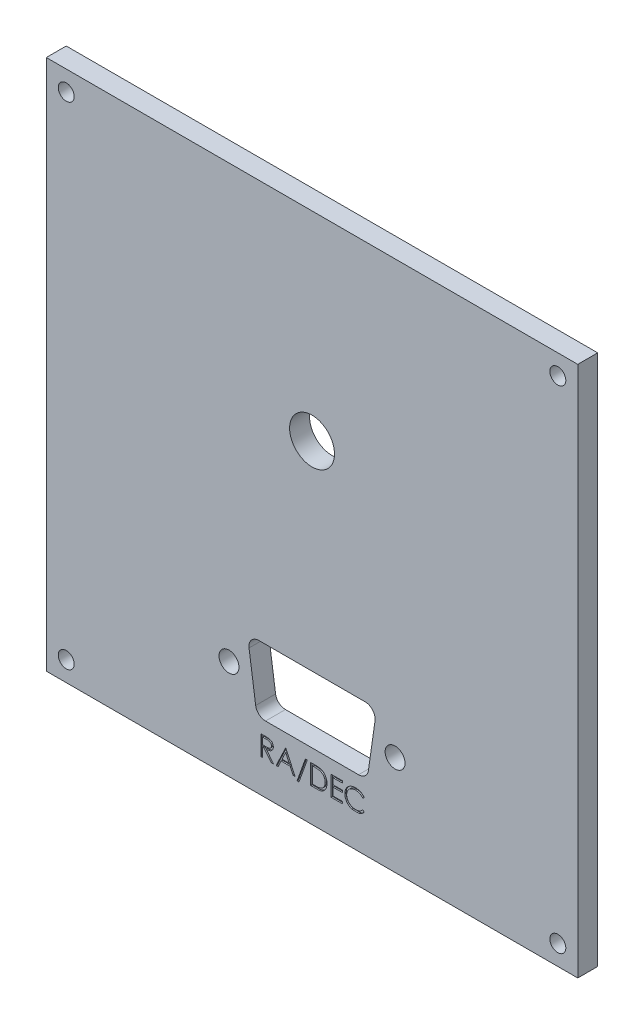
SolidWorks part; units mm, degrees
material "5052-O"
ref_plane "정면" through (0, 0, 0) normal (0, 0, 1) x (1, 0, 0)
ref_plane "윗면" through (0, 0, 0) normal (0, 1, 0) x (1, 0, 0)
ref_plane "우측면" through (0, 0, 0) normal (1, 0, 0) x (0, 0, -1)
sketch "스케치1" plane through (0, 0, 0) normal (0, 0, 1) x (1, 0, 0)
  line L1 (-40, 40) -> (40, 40)
  line L2 (-40, 40) -> (-40, -40)
  line L3 (-40, -40) -> (40, -40)
  line L4 (40, 40) -> (40, -40)
  line L5 (-40, 40) -> (40, -40) construction
  line L6 (-40, -40) -> (40, 40) construction
  point P0 (0, 0)
  dimension "D1" = 80
  dimension "D2" = 80
extrude "보스-돌출1" add sketch "스케치1" along normal blind 3
hole_wizard "M2 여유 구멍1" positions "스케치2" profile "스케치3" hole size "M2" standard "ISO" end condition through all
sketch "스케치2" plane through (0, 0, 3) normal (0, 0, 1) x (1, 0, 0)
  line L1 (-37, 37) -> (37, 37)
  line L2 (-37, 37) -> (-37, -37)
  line L3 (-37, -37) -> (37, -37)
  line L4 (37, 37) -> (37, -37)
  line L5 (40, 40) -> (-40, 40) construction
  line L6 (-40, 40) -> (-40, -40) construction
  point P0 (-37, 37)
  point P2 (-37, -37)
  point P4 (37, -37)
  point P6 (37, 37)
  point P92 (0, 37)
  point P93 (0, 40)
  point P94 (-37, 0)
  point P97 (-40, 0)
  dimension "D1" = 74
  dimension "D2" = 74
sketch "스케치3" plane through (-37, 37, 3) normal (1, 0, 0) x (0, -1, 0)
  line L0 (0, 0) -> (0, 3)
  line L1 (0, 3) -> (1.2, 3)
  line L2 (1.2, 3) -> (1.2, 0)
  line L5 (1.2, 0) -> (0, 0)
  line L11 (0, -6.35) -> (0, 107.95) construction
  dimension "관통 구멍 지름" = 2.4
  dimension "관통 구멍 깊이" = 3
hole_wizard "M3 여유 구멍1" positions "스케치4" profile "스케치5" hole size "M3" standard "ISO"
sketch "스케치4" plane through (0, 0, 3) normal (0, 0, 1) x (1, 0, 0)
  line L1 (5.1764, 29.3185) -> (-19.3185, 4.8236)
  line L2 (-19.3185, 4.8236) -> (14.1421, -4.1421)
  line L3 (14.1421, -4.1421) -> (5.1764, 29.3185)
  line L4 (5.1764, 29.3185) -> (-2.5882, 0.3407)
  line L7 (-40, 40) -> (-40, -40) construction
  line L8 (40, 40) -> (-40, 40) construction
  circle A0 centre (0, 10) radius 20 construction
  point P3 (5.1764, 29.3185)
  point P4 (-19.3185, 4.8236)
  point P5 (14.1421, -4.1421)
  point P27 (-5.1764, 127.2034)
  dimension "D1" = 40
  dimension "D2" = 15
  dimension "D3" = 30
sketch "스케치5" plane through (-5.1764, 127.2034, 3) normal (1, 0, 0) x (0, -1, 0)
  line L0 (0, 0) -> (0, 3)
  line L1 (0, 3) -> (1.6, 3)
  line L2 (1.6, 3) -> (1.6, 0)
  line L5 (1.6, 0) -> (0, 0)
  line L11 (0, -6.35) -> (0, 107.95) construction
  dimension "관통 구멍 지름" = 3.2
  dimension "관통 구멍 깊이" = 3
sketch "스케치6" plane through (0, 0, 3) normal (0, 0, 1) x (1, 0, 0)
  line L0 (-8, -20) -> (8, -20)
  line L1 (8.4849, -28.7121) -> (9.4849, -21.7121)
  line L2 (7, -30) -> (-7, -30)
  line L3 (-8.4849, -28.7121) -> (-9.4849, -21.7121)
  line L4 (-40, -40) -> (40, -40) construction
  line L5 (-12.5, -25) -> (12.5, -25)
  line L6 (0, -20) -> (0, -30)
  line L7 (40, -40) -> (40, 40) construction
  circle A0 centre (-8, -21.5) radius 1.5
  circle A1 centre (8, -21.5) radius 1.5
  circle A2 centre (-7, -28.5) radius 1.5
  circle A3 centre (7, -28.5) radius 1.5
  circle A4 centre (-12.5, -25) radius 1.5
  circle A5 centre (12.5, -25) radius 1.5
  point P18 (0, -25)
  dimension "D1" = 3
  dimension "D2" = 16
  dimension "D3" = 14
  dimension "D4" = 7
  dimension "D7" = 3
  dimension "D5" = 10
  dimension "D6" = 25
  dimension "D8" = 40
extrude "컷-돌출1" cut sketch "스케치6" against normal through all
sketch "스케치7" plane through (0, 0, 3) normal (0, 0, 1) x (1, 0, 0)
  line L0 (-10, -35) -> (10, -35)
  line L1 (-40, -40) -> (40, -40) construction
  line L2 (-7.7115, -32) -> (-7.1112, -32)
  line L3 (-6.8906, -33.6154) -> (-5.7885, -35)
  line L4 (-5.7885, -35) -> (-6.1214, -35)
  line L5 (-6.1214, -35) -> (-7.2236, -33.6154)
  line L6 (-7.2236, -33.6154) -> (-7.4423, -33.6154)
  line L7 (-7.4423, -33.6154) -> (-7.4423, -35)
  line L8 (-7.4423, -35) -> (-7.7115, -35)
  line L9 (-7.7115, -35) -> (-7.7115, -32)
  line L10 (-7.4423, -32.3077) -> (-7.4423, -33.3077)
  line L11 (-7.4423, -33.3077) -> (-6.893, -33.3119)
  line L12 (-6.8798, -32.3077) -> (-7.4423, -32.3077)
  line L13 (-3.9423, -32) -> (-2.5577, -35)
  line L14 (-2.5577, -35) -> (-2.8504, -35)
  line L15 (-2.8504, -35) -> (-3.2939, -34.0385)
  line L16 (-3.2939, -34.0385) -> (-4.6538, -34.0385)
  line L17 (-4.6538, -34.0385) -> (-5.11, -35)
  line L18 (-5.11, -35) -> (-5.4038, -35)
  line L19 (-5.4038, -35) -> (-3.9808, -32)
  line L20 (-3.9808, -32) -> (-3.9423, -32)
  line L21 (-3.9645, -32.5847) -> (-4.5078, -33.7308)
  line L22 (-4.5078, -33.7308) -> (-3.4357, -33.7308)
  line L23 (-3.4357, -33.7308) -> (-3.9645, -32.5847)
  line L24 (-0.7115, -31.9231) -> (-1.9663, -35.4231)
  line L25 (-1.9663, -35.4231) -> (-2.25, -35.4231)
  line L26 (-2.25, -35.4231) -> (-0.9952, -31.9231)
  line L27 (-0.9952, -31.9231) -> (-0.7115, -31.9231)
  line L28 (-0.2115, -35) -> (-0.2115, -32)
  line L29 (-0.2115, -32) -> (0.3942, -32)
  line L30 (0.7181, -35) -> (-0.2115, -35)
  line L31 (0.0577, -34.6923) -> (0.402, -34.6923)
  line L32 (0.2686, -32.3077) -> (0.0577, -32.3077)
  line L33 (0.0577, -32.3077) -> (0.0577, -34.6923)
  line L34 (2.8654, -32) -> (4.5577, -32)
  line L35 (4.5577, -32) -> (4.5577, -32.3077)
  line L36 (4.5577, -32.3077) -> (3.1346, -32.3077)
  line L37 (3.1346, -32.3077) -> (3.1346, -33.2308)
  line L38 (3.1346, -33.2308) -> (4.5577, -33.2308)
  line L39 (4.5577, -33.2308) -> (4.5577, -33.5385)
  line L40 (4.5577, -33.5385) -> (3.1346, -33.5385)
  line L41 (3.1346, -33.5385) -> (3.1346, -34.6923)
  line L42 (3.1346, -34.6923) -> (4.5577, -34.6923)
  line L43 (4.5577, -34.6923) -> (4.5577, -35)
  line L44 (4.5577, -35) -> (2.8654, -35)
  line L45 (2.8654, -35) -> (2.8654, -32)
  line L46 (7.8654, -32.5505) -> (7.6298, -32.7308)
  line L47 (7.6298, -34.2692) -> (7.8654, -34.4477)
  spline S0 degree 3 poles (-7.1112, -32) (-7.0343, -32.0004) (-6.924, -32.0002) (-6.7838, -32.0059) (-6.6938, -32.0094) (-6.6139, -32.0159) (-6.5272, -32.0234) (-6.4676, -32.0328) (-6.4315, -32.0409) knots 0 0 0 0 0.338434 0.484822 0.617158 0.734698 0.837385 1 1 1 1
  spline S1 degree 3 poles (-6.4315, -32.0409) (-6.3878, -32.0505) (-6.3243, -32.0705) (-6.244, -32.106) (-6.1876, -32.1368) (-6.1347, -32.1724) (-6.0847, -32.2122) (-6.0374, -32.256) (-5.9948, -32.3049) (-5.9545, -32.3562) (-5.9206, -32.4117) (-5.8913, -32.4697) (-5.868, -32.5308) (-5.8493, -32.5944) (-5.8313, -32.6848) (-5.8268, -32.7549) (-5.8269, -32.8023) knots 0 0 0 0 0.127064 0.188745 0.249132 0.309453 0.369827 0.43065 0.492352 0.554072 0.61569 0.676798 0.738439 0.801317 0.865185 1 1 1 1
  spline S2 degree 3 poles (-5.8269, -32.8023) (-5.8266, -32.8801) (-5.8399, -32.9957) (-5.8911, -33.139) (-5.9428, -33.2369) (-6.0086, -33.3251) (-6.0878, -33.4026) (-6.1802, -33.4674) (-6.2663, -33.5124) (-6.3423, -33.5412) (-6.4049, -33.5614) (-6.4732, -33.5771) (-6.5466, -33.5911) (-6.6252, -33.6017) (-6.7403, -33.6124) (-6.8295, -33.6152) (-6.8906, -33.6154) knots 0 0 0 0 0.153721 0.226714 0.299191 0.37119 0.443006 0.516689 0.593217 0.633873 0.676989 0.7229 0.771959 0.824211 0.879379 1 1 1 1
  spline S3 degree 3 poles (-6.893, -33.3119) (-6.8433, -33.3127) (-6.7714, -33.3101) (-6.6788, -33.3046) (-6.6171, -33.2987) (-6.5605, -33.291) (-6.5091, -33.2814) (-6.4629, -33.2702) (-6.409, -33.2529) (-6.3488, -33.2254) (-6.2834, -33.1855) (-6.2276, -33.1353) (-6.1806, -33.0779) (-6.1428, -33.0148) (-6.1069, -32.9237) (-6.096, -32.8507) (-6.0962, -32.8017) knots 0 0 0 0 0.138913 0.201185 0.259124 0.312255 0.360682 0.405086 0.445102 0.518778 0.589462 0.658462 0.727283 0.796322 0.863175 1 1 1 1
  spline S4 degree 3 poles (-6.0962, -32.8017) (-6.0963, -32.754) (-6.1062, -32.682) (-6.1441, -32.5937) (-6.1821, -32.5318) (-6.2284, -32.4757) (-6.2826, -32.4277) (-6.3434, -32.388) (-6.4002, -32.3627) (-6.451, -32.3472) (-6.4951, -32.3362) (-6.5449, -32.3274) (-6.6007, -32.3204) (-6.6622, -32.3144) (-6.7559, -32.3087) (-6.8291, -32.3075) (-6.8798, -32.3077) knots 0 0 0 0 0.136365 0.204019 0.273064 0.342913 0.410965 0.479169 0.549308 0.587652 0.630647 0.678879 0.731934 0.791111 0.855283 1 1 1 1
  spline S5 degree 3 poles (0.3942, -32) (0.496, -32.0004) (0.6432, -32.0026) (0.8319, -32.014) (0.9566, -32.0259) (1.0701, -32.0407) (1.1998, -32.0639) (1.2904, -32.0884) (1.3462, -32.1082) knots 0 0 0 0 0.317406 0.458844 0.589367 0.707831 0.81577 1 1 1 1
  spline S6 degree 3 poles (1.3462, -32.1082) (1.4153, -32.1327) (1.5155, -32.1775) (1.6392, -32.2528) (1.726, -32.3153) (1.8055, -32.3863) (1.8809, -32.4626) (1.9492, -32.5471) (2.0117, -32.638) (2.068, -32.7343) (2.117, -32.8357) (2.1577, -32.9418) (2.1915, -33.0522) (2.218, -33.1672) (2.2428, -33.3292) (2.2504, -33.4537) (2.25, -33.5379) knots 0 0 0 0 0.121694 0.181155 0.239875 0.298702 0.357647 0.417605 0.478494 0.540407 0.602345 0.665004 0.728559 0.793651 0.860534 1 1 1 1
  spline S7 degree 3 poles (2.25, -33.5379) (2.2503, -33.611) (2.2439, -33.7189) (2.225, -33.8602) (2.2035, -33.961) (2.1775, -34.059) (2.1441, -34.1531) (2.1058, -34.2443) (2.0612, -34.3312) (2.0122, -34.4136) (1.9597, -34.4912) (1.9036, -34.563) (1.8434, -34.6292) (1.78, -34.6897) (1.7128, -34.745) (1.6418, -34.794) (1.5673, -34.8386) (1.487, -34.8775) (1.3994, -34.9105) (1.3043, -34.9378) (1.2017, -34.9606) (1.0916, -34.9786) (0.9297, -34.9953) (0.8042, -35.0005) (0.7181, -35) knots 0 0 0 0 0.090807 0.134295 0.177024 0.218823 0.260244 0.30108 0.341614 0.381583 0.42012 0.458075 0.494738 0.531195 0.566934 0.602713 0.638327 0.674853 0.713467 0.754442 0.797815 0.843989 0.893072 1 1 1 1
  spline S8 degree 3 poles (0.402, -34.6923) (0.4972, -34.6923) (0.6341, -34.6904) (0.8086, -34.6822) (0.9218, -34.674) (1.0232, -34.6631) (1.1354, -34.6481) (1.2128, -34.6307) (1.2596, -34.616) knots 0 0 0 0 0.330628 0.475549 0.606746 0.725024 0.829742 1 1 1 1
  spline S9 degree 3 poles (1.2596, -34.616) (1.3139, -34.5976) (1.3937, -34.5669) (1.4917, -34.5113) (1.5603, -34.4656) (1.624, -34.4136) (1.6835, -34.3565) (1.7387, -34.2941) (1.789, -34.2264) (1.834, -34.1538) (1.873, -34.077) (1.9072, -33.997) (1.934, -33.9124) (1.955, -33.824) (1.9753, -33.6989) (1.9808, -33.6025) (1.9808, -33.5373) knots 0 0 0 0 0.123338 0.183125 0.241783 0.300579 0.35968 0.418882 0.479531 0.540851 0.602303 0.664463 0.727806 0.792895 0.859672 1 1 1 1
  spline S10 degree 3 poles (1.9808, -33.5373) (1.9816, -33.4683) (1.9744, -33.3667) (1.9527, -33.2348) (1.9298, -33.1414) (1.9005, -33.0517) (1.864, -32.9661) (1.8223, -32.8839) (1.7727, -32.8067) (1.7183, -32.7338) (1.658, -32.667) (1.5926, -32.6061) (1.523, -32.5503) (1.4471, -32.5017) (1.3386, -32.443) (1.2506, -32.4105) (1.1905, -32.3918) knots 0 0 0 0 0.137813 0.203226 0.267174 0.330024 0.391794 0.453084 0.514334 0.575 0.634865 0.694116 0.753442 0.813126 0.87408 1 1 1 1
  spline S11 degree 3 poles (1.1905, -32.3918) (1.1373, -32.3757) (1.0504, -32.3575) (0.9263, -32.3397) (0.8167, -32.3276) (0.6958, -32.319) (0.5119, -32.3099) (0.3682, -32.3074) (0.2686, -32.3077) knots 0 0 0 0 0.179285 0.286583 0.405111 0.535593 0.67819 1 1 1 1
  spline S12 degree 3 poles (7.6298, -32.7308) (7.597, -32.6905) (7.5451, -32.6329) (7.4699, -32.5628) (7.4117, -32.5137) (7.3502, -32.4696) (7.2869, -32.4282) (7.2207, -32.3911) (7.1292, -32.3462) (7.0095, -32.2993) (6.806, -32.2458) (6.647, -32.2302) (6.5397, -32.2308) knots 0 0 0 0 0.125475 0.187121 0.248294 0.309295 0.36985 0.430973 0.492456 0.616148 0.740844 1 1 1 1
  spline S13 degree 3 poles (6.5397, -32.2308) (6.4798, -32.23) (6.3906, -32.2364) (6.2737, -32.2537) (6.1882, -32.2726) (6.1046, -32.2966) (6.0222, -32.3253) (5.9423, -32.3607) (5.8638, -32.3999) (5.7886, -32.4441) (5.7174, -32.4924) (5.6505, -32.5442) (5.5879, -32.5996) (5.5294, -32.6584) (5.4756, -32.7213) (5.4266, -32.788) (5.3814, -32.8577) (5.3409, -32.9302) (5.3071, -33.0057) (5.2771, -33.0829) (5.2533, -33.1628) (5.2345, -33.2446) (5.217, -33.3579) (5.2108, -33.4445) (5.2115, -33.503) knots 0 0 0 0 0.087502 0.130463 0.172752 0.215403 0.25765 0.300153 0.343121 0.385925 0.427686 0.468818 0.509492 0.549883 0.58998 0.630405 0.670869 0.711384 0.751627 0.791776 0.832459 0.873319 0.914543 1 1 1 1
  spline S14 degree 3 poles (5.2115, -33.503) (5.2111, -33.5901) (5.2233, -33.7187) (5.2624, -33.8841) (5.3054, -34.0001) (5.3585, -34.1115) (5.4255, -34.2162) (5.5032, -34.316) (5.5926, -34.4085) (5.6907, -34.4929) (5.7959, -34.5673) (5.908, -34.6293) (6.0257, -34.6808) (6.15, -34.7204) (6.3272, -34.7585) (6.4649, -34.77) (6.5583, -34.7692) knots 0 0 0 0 0.12629 0.186726 0.246146 0.305576 0.365429 0.426326 0.48884 0.551725 0.613919 0.675484 0.737334 0.800229 0.864502 1 1 1 1
  spline S15 degree 3 poles (6.5583, -34.7692) (6.6613, -34.7693) (6.8143, -34.7547) (7.0096, -34.7016) (7.1479, -34.6469) (7.2793, -34.5757) (7.4487, -34.4588) (7.5606, -34.3488) (7.6298, -34.2692) knots 0 0 0 0 0.252949 0.374755 0.49594 0.617181 0.740909 1 1 1 1
  spline S16 degree 3 poles (7.8654, -34.4477) (7.8283, -34.497) (7.7693, -34.5679) (7.6828, -34.6545) (7.6146, -34.7146) (7.5433, -34.7713) (7.4678, -34.823) (7.3891, -34.8704) (7.3073, -34.9138) (7.2227, -34.9523) (7.1353, -34.9853) (7.0454, -35.0136) (6.9531, -35.037) (6.8582, -35.0552) (6.7273, -35.0718) (6.6273, -35.0774) (6.5601, -35.0769) knots 0 0 0 0 0.123053 0.183475 0.243727 0.304279 0.364863 0.425946 0.487391 0.54922 0.611144 0.673529 0.736961 0.800785 0.866013 1 1 1 1
  spline S17 degree 3 poles (6.5601, -35.0769) (6.4963, -35.0777) (6.4019, -35.0726) (6.2781, -35.0592) (6.1892, -35.0445) (6.1025, -35.027) (6.0189, -35.0037) (5.9375, -34.9775) (5.8587, -34.9467) (5.7823, -34.912) (5.7087, -34.8727) (5.6379, -34.8293) (5.5691, -34.7826) (5.5035, -34.7312) (5.4188, -34.6569) (5.3596, -34.5957) (5.3227, -34.5523) knots 0 0 0 0 0.13775 0.203917 0.26878 0.332414 0.394754 0.45618 0.516996 0.577396 0.637198 0.696999 0.756756 0.816554 0.876948 1 1 1 1
  spline S18 degree 3 poles (5.3227, -34.5523) (5.2605, -34.4797) (5.177, -34.3633) (5.0886, -34.195) (5.0351, -34.0635) (4.9934, -33.9263) (4.954, -33.7331) (4.942, -33.5836) (4.9423, -33.4826) knots 0 0 0 0 0.247156 0.36878 0.490734 0.613614 0.738958 1 1 1 1
  spline S19 degree 3 poles (4.9423, -33.4826) (4.9423, -33.3765) (4.9557, -33.2192) (5.0044, -33.0174) (5.0553, -32.8749) (5.1199, -32.7385) (5.1996, -32.6092) (5.2936, -32.4862) (5.4011, -32.3713) (5.519, -32.2663) (5.6453, -32.1739) (5.7797, -32.097) (5.9207, -32.0327) (6.0694, -31.9833) (6.2808, -31.9363) (6.4452, -31.9233) (6.5565, -31.9231) knots 0 0 0 0 0.127014 0.187955 0.248014 0.307748 0.368235 0.42947 0.492743 0.556258 0.618217 0.679655 0.741246 0.803415 0.866815 1 1 1 1
  spline S20 degree 3 poles (6.5565, -31.9231) (6.6247, -31.9229) (6.7259, -31.9276) (6.8584, -31.9456) (6.9541, -31.9637) (7.0476, -31.9861) (7.1383, -32.0154) (7.2266, -32.0489) (7.3121, -32.0874) (7.3944, -32.1307) (7.4733, -32.1782) (7.5482, -32.2298) (7.6198, -32.2853) (7.6867, -32.3456) (7.7727, -32.4306) (7.8292, -32.5019) (7.8654, -32.5505) knots 0 0 0 0 0.135683 0.201215 0.265682 0.329267 0.392395 0.45507 0.517127 0.57879 0.63974 0.700192 0.759806 0.819628 0.879355 1 1 1 1
  point P1 (0, -35)
  dimension "D1" = 20
  dimension "D2" = 5
extrude "컷-돌출2" cut sketch "스케치7" against normal blind 0.2 contours S2 S1 S0 L2 L9 L0 L7 L6 L5 L3 S4 S3 L11 L10 L12 | L20 L19 L0 L17 L16 L15 L13 L23 L22 L21 | S7 S6 S5 L29 L28 L0 S11 S10 S9 S8 L31 L33 L32 | S20 S19 S18 S17 L0 S16 L47 S15 S14 S13 S12 L46 | L45 L0 L43 L42 L41 L40 L39 L38 L37 L36 L35 L34 | L27 L26 L0 L24 | L26 L25 L24 L0
hole_wizard "1/4 여유 구멍1" positions "스케치8" profile "스케치9" hole size "1/4" standard "Ansi Inch" end condition through all
sketch "스케치8" plane through (0, 0, 3) normal (0, 0, 1) x (1, 0, 0)
  line L0 (40, 40) -> (-40, 40) construction
  point P0 (0, 10)
  point P3 (0, 0)
  point P6 (0, 0)
  dimension "D1" = 30
sketch "스케치9" plane through (0, 10, 3) normal (1, 0, 0) x (0, -1, 0)
  line L0 (0, 0) -> (0, 3)
  line L1 (0, 3) -> (3.3782, 3)
  line L2 (3.3782, 3) -> (3.3782, 0)
  line L5 (3.3782, 0) -> (0, 0)
  line L11 (0, -6.35) -> (0, 107.95) construction
  dimension "관통 구멍 지름" = 6.7564
  dimension "관통 구멍 깊이" = 3
equation "\"D2@스케치1\"=\"D1@스케치1\""
equation "\"D2@스케치2\"=\"D1@스케치2\""
